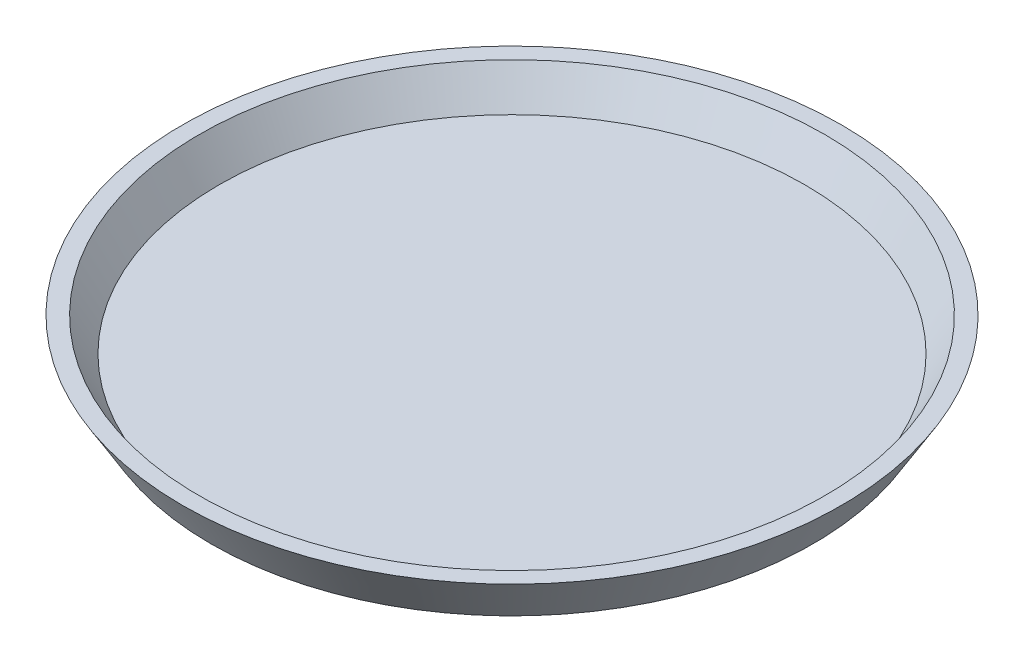
SolidWorks part; units mm, degrees
ref_plane "Front Plane" through (0, 0, 0) normal (0, 0, 1) x (1, 0, 0)
ref_plane "Top Plane" through (0, 0, 0) normal (0, 1, 0) x (1, 0, 0)
ref_plane "Right Plane" through (0, 0, 0) normal (1, 0, 0) x (0, 0, -1)
sketch "Sketch1" plane through (0, 0, 0) normal (0, 0, 1) x (1, 0, 0)
  line L0 (0, 0) -> (63, 0)
  line L1 (63, 0) -> (69, 10)
  line L6 (0, 3) -> (61.3014, 3)
  line L7 (61.3014, 3) -> (65.5014, 10)
  line L8 (69, 10) -> (65.5014, 10)
  line L9 (0, 0) -> (0, 3)
  line L10 (61.3014, 3) -> (66.4275, 11.5435) construction
  dimension "D1" = 69
  dimension "D2" = 63
  dimension "D3" = 10
  dimension "D4" = 3
revolve "Revolve1" add sketch "Sketch1" angle 360 about L9
